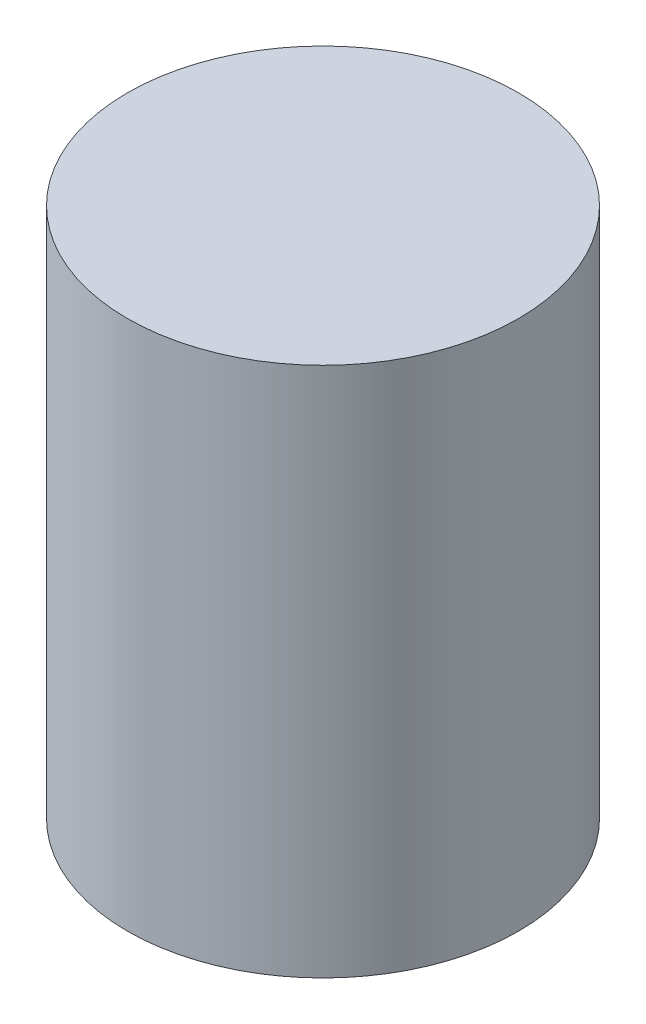
SolidWorks part; units mm, degrees
ref_plane "Front Plane" through (0, 0, 0) normal (0, 0, 1) x (1, 0, 0)
ref_plane "Top Plane" through (0, 0, 0) normal (0, 1, 0) x (1, 0, 0)
ref_plane "Right Plane" through (0, 0, 0) normal (1, 0, 0) x (0, 0, -1)
sketch "Sketch1" plane through (0, 0, 0) normal (0, 1, 0) x (1, 0, 0)
  circle A0 centre (-22.7706, 24.3231) radius 11
extrude "Boss-Extrude2" add sketch "Sketch1" along normal blind 29.85
